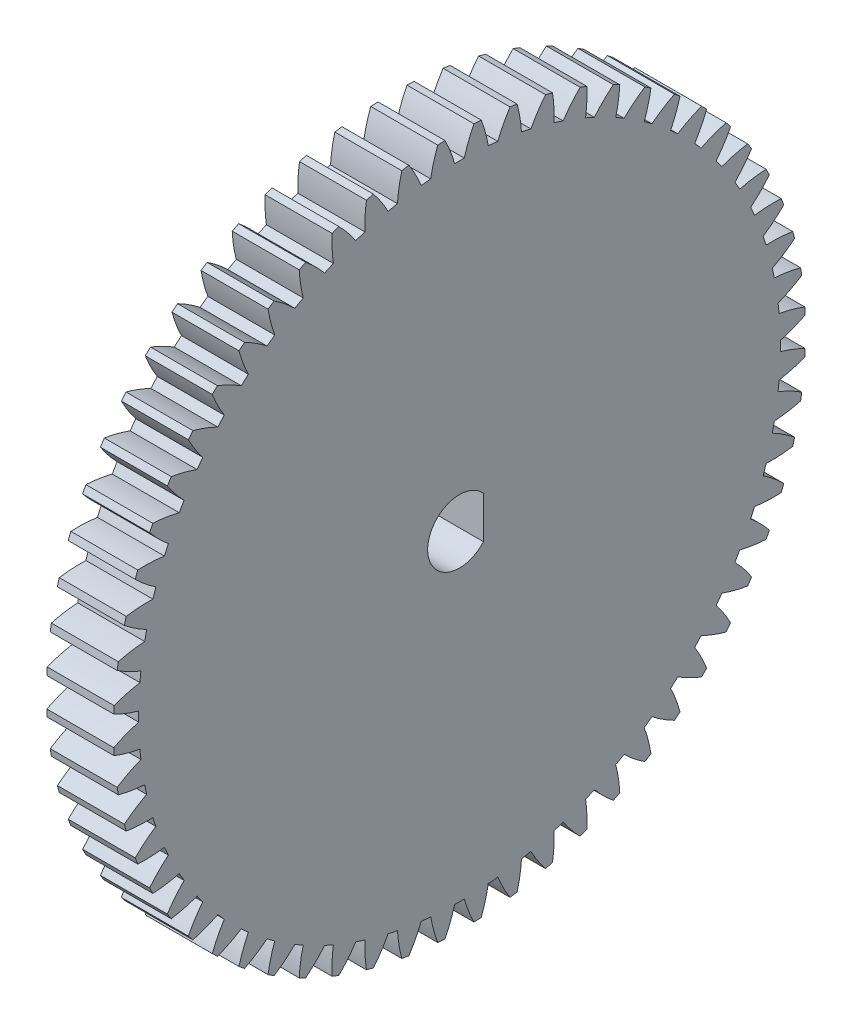
SolidWorks part; units mm, degrees
ref_plane "Plane1" through (0, 0, 0) normal (0, 0, 1) x (1, 0, 0)
ref_plane "Plane2" through (0, 0, 0) normal (0, 1, 0) x (1, 0, 0)
ref_plane "Plane3" through (0, 0, 0) normal (1, 0, 0) x (0, 0, -1)
sketch "HoldingSke" plane through (0, 0, 0) normal (0, 1, 0) x (1, 0, 0)
  line L0 (0, 0) -> (0.5, -0.866)
  line L1 (-15, 0) -> (100, 0) construction
  line L2 (0, 0) -> (-2.1039, 2.3779)
  line L3 (0, 0) -> (-11.863, 4.5341)
  line L4 (0, 0) -> (4.318, 7.479)
  line L5 (0, 0) -> (-46.8476, -17.4728)
  line L6 (0, 0) -> (-4.9738, -3.3558)
  line L7 (-2.1039, 2.3779) -> (8.6587, 51.2064)
  line L8 (-76.2, 54.61) -> (-75.2, 54.61)
  line L9 (-71.009, 38.7566) -> (-53.1078, 45.2721)
  line L10 (-76.2, 71.12) -> (104.1128, 71.12)
  line L11 (0, 0) -> (-6, 0)
  line L12 (-76.2, 101.6) -> (-76.162, 101.6)
  line L13 (24.9733, 27.94) -> (52.9518, 28.4284)
  line L14 (24.9733, 27.94) -> (24.9743, 27.94)
  line L15 (24.9733, 27.94) -> (100.4006, 29.5858)
  line L16 (-63.627, -1) -> (-12.827, -1)
  circle A0 centre (0, 0) radius 3
  circle A1 centre (0, 0) radius 28.749
  circle A2 centre (0, 0) radius 37.5
  circle A3 centre (0, 0) radius 3
  dimension "MHD" = 57.498
  dimension "Hub_dia" = 75
  dimension "Bore" = 6
  dimension "MBD" = 6
  dimension "Num_teeth" = 60
  dimension "Pitch" = 1
  dimension "Overall_len" = 50
  dimension "Show_teeth" = 60
  dimension "Thickness" = 6
  dimension "OAL" = 50.0006
  dimension "T_dim" = 1
  dimension "Ap" = 20
  dimension "H" = 19.05
  dimension "Pitch_radius" = 180.3128
  dimension "Width" = 6
  dimension "Backlash" = 0.038
  dimension "Addendum_fac" = 1
  dimension "Dedendum_fac" = 1.25
  dimension "Clearance_fac" = 0.25
  dimension "Dedendum_add" = 0.001
  dimension "Module" = 1
sketch "BasProSke" plane through (0, 0, 0) normal (0, 1, 0) x (1, 0, 0)
  line L0 (-10, 0) -> (60, 0) construction
  line L1 (0, 0) -> (0, 31)
  line L2 (0, 0) -> (6, 0)
  line L3 (6, 0) -> (6, 31)
  line L4 (6, 31) -> (0, 31)
  dimension "Thickness" = 6
  dimension "Diameter" = 62
revolve "Base-Revolve" add sketch "BasProSke" angle 360 about L0
sketch "TooCutSke" plane through (0, 0, 0) normal (1, 0, 0) x (0, 0, -1)
  line L1 (0, 0) -> (0, 107) construction
  line L2 (0, 0) -> (-0.8518, 29.9879) construction
  line L3 (0, 0) -> (-3.1393, 59.9006) construction
  line L4 (-0.8518, 29.9879) -> (-1.5696, 29.9503) construction
  arc A0 (0.4302, 28.7458) -> (-0.4302, 28.7458) centre (0, 0) ccw
  arc A1 (1.3127, 30.9976) -> (-1.3127, 30.9976) centre (0, 0) ccw
  circle A2 centre (0, 0) radius 30 construction
  circle A3 centre (0, 0) radius 28.1908 construction
  arc A4 (-0.4302, 28.7458) -> (-1.3127, 30.9976) centre (-11.9871, 25.5153) ccw
  arc A5 (1.3127, 30.9976) -> (0.4302, 28.7458) centre (11.9871, 25.5153) ccw
  dimension "Root_dia" = 57.498
  dimension "Overcut_dia" = 62.0508
  dimension "Pitch_dia" = 60
  dimension "Base_dia" = 56.3816
  dimension "Flank_rad" = 12
  dimension "Half_ang" = 3
  dimension "Half_CT" = 0.7188
extrude "ToothCut" cut sketch "TooCutSke" along normal through all
fillet "Breaks" [suppressed] radius 0.02
fillet "RootFillets" [suppressed] radius 0.251
pattern_circular "TeethCuts" count 60 every 6 about axis through (-10, 0, 0) along (1, 0, 0) of "ToothCut", "RootFillets", "Breaks"
sketch "HubNeaOneSke" plane through (0, 0, 0) normal (-1, 0, 0) x (0, 0, 1)
  circle A0 centre (0, 0) radius 28.749
  dimension "Diameter" = 57.498
extrude "HubNearOne" [suppressed] add sketch "HubNeaOneSke" along normal blind 44.0006
sketch "HubNeaBotSke" plane through (0, 0, 0) normal (-1, 0, 0) x (0, 0, 1)
  circle A0 centre (0, 0) radius 28.749
  dimension "Diameter" = 57.498
extrude "HubNearBoth" [suppressed] add sketch "HubNeaBotSke" along normal blind 22.0003
ref_plane "FarPln" through (6, 0, 0) normal (1, 0, 0) x (0, 0, -1)
sketch "HubFarSke" plane through (6, 0, 0) normal (1, 0, 0) x (0, 0, -1)
  circle A0 centre (0, 0) radius 28.749
  dimension "Diameter" = 57.498
extrude "HubFar" [suppressed] add sketch "HubFarSke" along normal blind 22.0003
sketch "KeySke" plane through (0, 0, 0) normal (1, 0, 0) x (0, 0, -1)
  line L0 (-1, 0) -> (-1, 4)
  line L1 (-1, 4) -> (1, 4)
  line L2 (1, 4) -> (1, 0)
  line L3 (0, 0) -> (0, 34) construction
  line L4 (-1, 0) -> (1, 0)
  dimension "Offset" = 4
  dimension "Width" = 2
extrude "Keyway" [suppressed] cut sketch "KeySke" along normal mid plane 100.0011
pattern_circular "Keyway2" [suppressed] count 2 every 90 about axis through (-10, 0, 0) along (1, 0, 0)
sketch "Sketch1" plane through (6, 0, 0) normal (1, 0, 0) x (0, 0, -1)
  line L0 (2.1464, 1.875) -> (2.1464, -1.875)
  arc A0 (2.1464, 1.875) -> (2.1464, -1.875) centre (0, 0) ccw
  dimension "D1" = 5.7
  dimension "D2" = 3.75
extrude "Cut-Extrude1" cut sketch "Sketch1" against normal through all
equation "' \"Module@HoldingSke\" = 6.35"
equation "' \"Num_teeth@HoldingSke\" = 12"
equation "' \"Ap@HoldingSke\" =  20"
equation "' \"Ap@HoldingSke\" = 20"
equation "' \"Width@HoldingSke\" = 0.5 * 25.4"
equation "' \"Hub_dia@HoldingSke\"= 1 * 25.4"
equation "' \"Hub_dia@HoldingSke\" = 1 * 25.4"
equation "' \"Overall_len@HoldingSke\" = 1.0 * 25.4"
equation "' \"Bore@HoldingSke\" = 0.75 * 25.4"
equation "' \"T_dim@HoldingSke\" = 0.1 * 25.4"
equation "' \"Width@KeySke\" = 0.25 * 25.4"
equation "' \"Show_teeth@HoldingSke\" = 13"
equation "' \"Backlash@HoldingSke\" = 0.009 * 25.4"
equation "' \"Addendum_fac@HoldingSke\" = 1.0"
equation "' \"Dedendum_fac@HoldingSke\" = 1.25"
equation "' \"Dedendum_add@HoldingSke\" = 0.00005 * 25.4"
equation "' \"Clearance_fac@HoldingSke\" = 0.25"
equation "\"Pitch@HoldingSke\" = 1 / \"Module@HoldingSke\""
equation "\"Overcut_dia@TooCutSke\" = (\"Num_teeth@HoldingSke\" + 2 * \"Addendum_fac@HoldingSke\") / \"Pitch@HoldingSke\" + 0.002 * 25.4"
equation "\"Pitch_dia@TooCutSke\" = \"Num_teeth@HoldingSke\" / \"Pitch@HoldingSke\""
equation "\"Base_dia@TooCutSke\" = \"Num_teeth@HoldingSke\" / \"Pitch@HoldingSke\" * cos((\"Ap@HoldingSke\"  * 3.14159265 / 180))"
equation "\"Root_dia@TooCutSke\" = (\"Num_teeth@HoldingSke\" + 2) / \"Pitch@HoldingSke\" - 2 * (\"Addendum_fac@HoldingSke\" + \"Dedendum_fac@HoldingSke\") / \"Pitch@HoldingSke\" - \"Dedendum_add@HoldingSke\" * 2"
equation "\"Half_ang@TooCutSke\" = 180 / \"Num_teeth@HoldingSke\""
equation "\"Half_CT@TooCutSke\" = \"Num_teeth@HoldingSke\" / \"Pitch@HoldingSke\" * sin((3.14159265 / 2 / \"Num_teeth@HoldingSke\")) / 2 - 7 * \"Backlash@HoldingSke\" / 4"
equation "\"Flank_rad@TooCutSke\" = \"Num_teeth@HoldingSke\" / \"Pitch@HoldingSke\" / 5"
equation "\"Radius@RootFillets\" = \"Clearance_fac@HoldingSke\" / \"Pitch@HoldingSke\" + \"Dedendum_add@HoldingSke\""
equation "\"Break_rad@Breaks\" = 0.02 / \"Pitch@HoldingSke\""
equation "\"Thickness@HoldingSke\" = \"Width@HoldingSke\""
equation "\"OAL@HoldingSke\" = \"Thickness@HoldingSke\""
equation "\"MHD@HoldingSke\" = (\"Num_teeth@HoldingSke\" + 2) / \"Pitch@HoldingSke\" - 2 * (\"Addendum_fac@HoldingSke\" + \"Dedendum_fac@HoldingSke\")  / \"Pitch@HoldingSke\" - \"Dedendum_add@HoldingSke\" * 2"
equation "\"MBD@HoldingSke\" = (\"Num_teeth@HoldingSke\" + 2) / \"Pitch@HoldingSke\" - 2 * (\"Addendum_fac@HoldingSke\" + \"Dedendum_fac@HoldingSke\")  / \"Pitch@HoldingSke\" - \"Dedendum_add@HoldingSke\" * 2 - 0.002 * 25.4"
equation "\"MHD@HoldingSke\" = ((sgn( \"MHD@HoldingSke\" - \"Hub_dia@HoldingSke\" )-1)*( \"MHD@HoldingSke\" - \"Hub_dia@HoldingSke\" ))/-2+ \"Hub_dia@HoldingSke\""
equation "\"MBD@HoldingSke\" = ((sgn( \"MBD@HoldingSke\" - \"Bore@HoldingSke\" )-1)*( \"MBD@HoldingSke\" - \"Bore@HoldingSke\" ))/-2+ \"Bore@HoldingSke\""
equation "\"OAL@HoldingSke\" = ((sgn( \"OAL@HoldingSke\" - \"Overall_len@HoldingSke\" )+1)*( \"OAL@HoldingSke\" - \"Overall_len@HoldingSke\" ))/2 + \"Overall_len@HoldingSke\" + 0.000002 * 25.4"
equation "\"Num_teeth@TeethCuts\" = int( \"Show_teeth@HoldingSke\" ) + 1"
equation "\"Num_teeth@TeethCuts\" = ((sgn( \"Num_teeth@TeethCuts\" - \"Num_teeth@HoldingSke\" )-1)*( \"Num_teeth@TeethCuts\" - \"Num_teeth@HoldingSke\" ))/-2+ \"Num_teeth@HoldingSke\""
equation "\"Num_teeth@TeethCuts\" = ((sgn( \"Num_teeth@TeethCuts\" - 2.0)+1)*( \"Num_teeth@TeethCuts\" - 2.0))/2 +2.0"
equation "\"Angle@TeethCuts\" = 360.0 / \"Num_teeth@HoldingSke\""
equation "\"Diameter@BasProSke\" = (\"Num_teeth@HoldingSke\" + 2 * \"Addendum_fac@HoldingSke\") / \"Pitch@HoldingSke\""
equation "\"Thickness@BasProSke\"  = \"Thickness@HoldingSke\""
equation "' \"Fillet_rad@BasProSke\" =  \"Thickness@HoldingSke\" * 0.05"
equation "' \"Fillet_rad@BasProSke\" = \"Thickness@HoldingSke\" * 0.05"
equation "\"MHD@HoldingSke\" = ((sgn( \"MHD@HoldingSke\" - \"Root_dia@TooCutSke\" )-1)*( \"MHD@HoldingSke\" - \"Root_dia@TooCutSke\" ))/-2+ \"Root_dia@TooCutSke\""
equation "\"Diameter@HubNeaOneSke\" = \"MHD@HoldingSke\""
equation "\"Length@HubNearOne\" = \"OAL@HoldingSke\" - \"Thickness@BasProSke\""
equation "\"Diameter@HubNeaBotSke\" = \"MHD@HoldingSke\""
equation "\"Length@HubNearBoth\" = ( \"OAL@HoldingSke\" - \"Thickness@BasProSke\" ) / 2.0"
equation "\"Thickness@FarPln\" = \"Thickness@BasProSke\""
equation "\"Diameter@HubFarSke\" = \"MHD@HoldingSke\""
equation "\"Length@HubFar\" = ( \"OAL@HoldingSke\" - \"Thickness@BasProSke\" ) / 2.0"
equation "\"D1@Keyway\" = \"OAL@HoldingSke\" * 2.0"
equation "\"Offset@KeySke\" = \"T_dim@HoldingSke\" + \"MBD@HoldingSke\" / 2.0"
